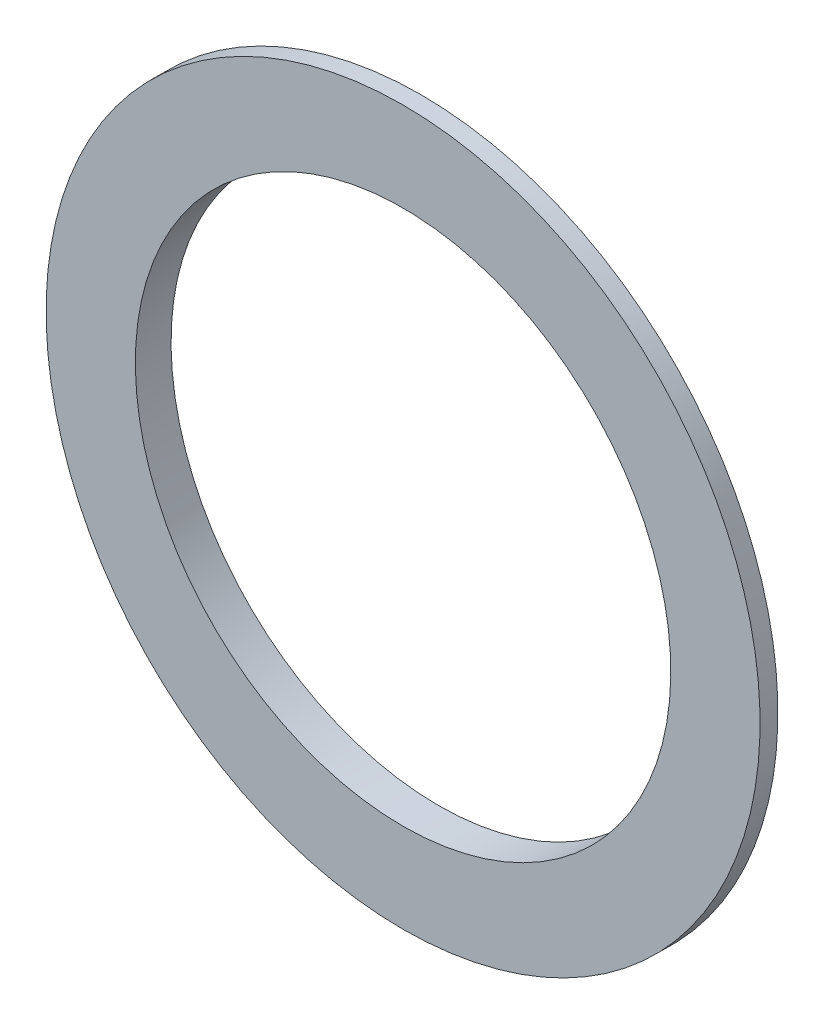
SolidWorks part; units mm, degrees
ref_plane "Front Plane" through (0, 0, 0) normal (0, 0, 1) x (1, 0, 0)
ref_plane "Top Plane" through (0, 0, 0) normal (0, 1, 0) x (1, 0, 0)
ref_plane "Right Plane" through (0, 0, 0) normal (1, 0, 0) x (0, 0, -1)
sketch "Sketch1" plane through (0, 0, 0) normal (1, 0, 0) x (0, 0, -1)
  line L0 (-3.175, 0) -> (3.175, 0) construction
  line L1 (-3.175, 47.625) -> (3.175, 47.625)
  line L2 (-3.175, 47.625) -> (-3.175, 63.5)
  line L3 (-3.175, 63.5) -> (0, 63.5)
  line L4 (0, 63.5) -> (0, 57.15)
  line L5 (0, 57.15) -> (3.175, 57.15)
  line L6 (3.175, 57.15) -> (3.175, 53.975)
  line L7 (3.175, 53.975) -> (0, 53.975)
  line L8 (0, 53.975) -> (0, 50.8)
  line L9 (0, 50.8) -> (3.175, 50.8)
  line L10 (3.175, 50.8) -> (3.175, 47.625)
  point P3 (0, 0)
  point P6 (-3.175, 57.7568)
  point P15 (0.9227, 53.975)
  dimension "D1" = 6.35
  dimension "D2" = 47.625
  dimension "D3" = 3.175
  dimension "D4" = 3.175
  dimension "D5" = 63.5
revolve "Revolve1" add sketch "Sketch1" angle 360 about L0
